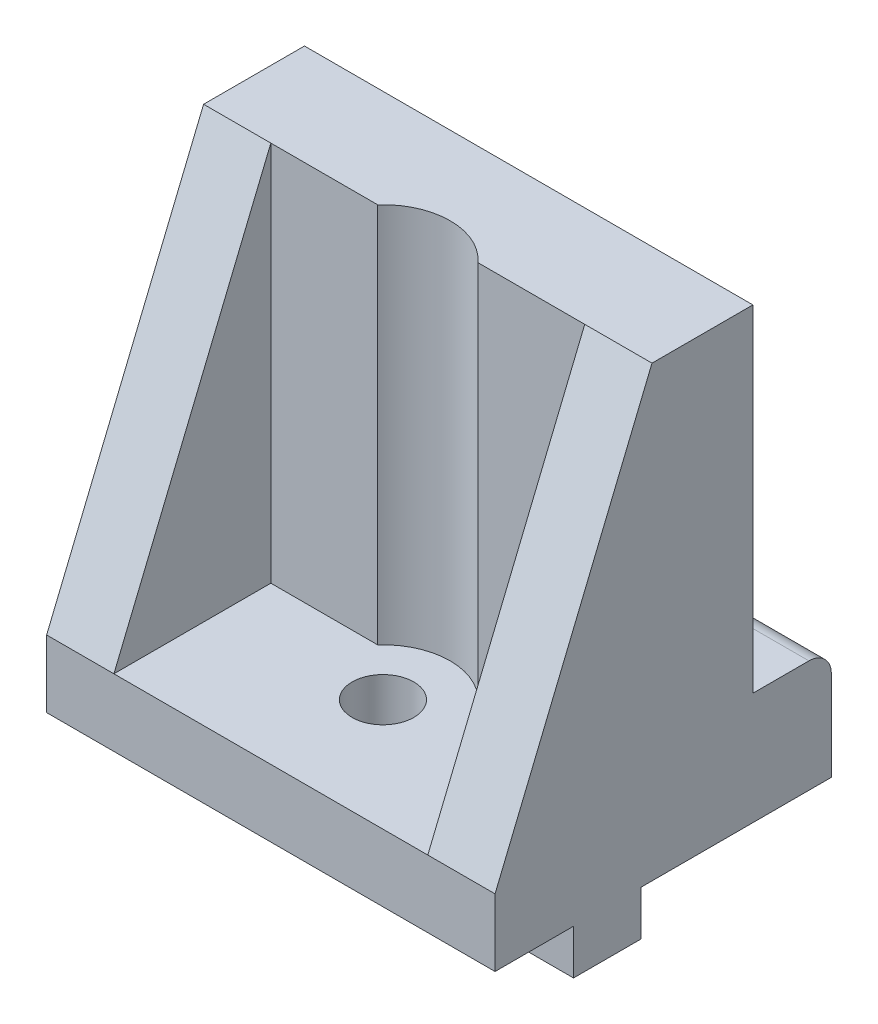
SolidWorks part; units mm, degrees
ref_plane "Alzado" through (0, 0, 0) normal (0, 0, 1) x (1, 0, 0)
ref_plane "Planta" through (0, 0, 0) normal (0, 1, 0) x (1, 0, 0)
ref_plane "Vista lateral" through (0, 0, 0) normal (1, 0, 0) x (0, 0, -1)
sketch "Croquis1" plane through (0, 0, 0) normal (0, 0, 1) x (1, 0, 0)
  line L1 (0, 0) -> (40, 0)
  line L2 (0, 0) -> (0, -40)
  line L3 (0, -40) -> (40, -40)
  line L4 (40, 0) -> (40, -40)
  dimension "D1" = 40
  dimension "D2" = 40
extrude "Saliente-Extruir1" add sketch "Croquis1" along normal blind 20
sketch "Croquis2" plane through (0, 0, 0) normal (0, 1, 0) x (1, 0, 0)
  line L0 (40, -20) -> (0, -20) construction
  line L1 (6, -20) -> (34, -20)
  line L2 (6, -20) -> (6, -6)
  line L3 (6, -6) -> (34, -6)
  line L4 (34, -20) -> (34, -6)
  line L5 (0, -20) -> (0, 0) construction
  line L6 (40, -20) -> (40, 0) construction
  line L7 (40, 0) -> (0, 0) construction
  dimension "D1" = 6
  dimension "D2" = 6
  dimension "D3" = 6
extrude "Cortar-Extruir1" cut sketch "Croquis2" against normal blind 34
sketch "Croquis3" plane through (0, 0, 0) normal (-1, 0, 0) x (0, 0, 1)
  line L0 (20, 0) -> (20, -34)
  line L1 (20, 0) -> (20, -40) construction
  line L2 (20, -34) -> (6, 0)
  line L3 (20, 0) -> (0, 0) construction
  line L4 (6, 0) -> (20, 0)
  dimension "D1" = 14
  dimension "D2" = 34
extrude "Cortar-Extruir2" cut sketch "Croquis3" against normal up to surface (40 mm away) up to face at (40, -20, 10)
sketch "Croquis7" plane through (0, -40, 0) normal (0, -1, 0) x (1, 0, 0)
  line L0 (0, 20) -> (0, 0) construction
  line L1 (0, 13) -> (40, 13)
  line L2 (0, 13) -> (0, 7)
  line L3 (0, 7) -> (40, 7)
  line L4 (40, 13) -> (40, 7)
  line L5 (40, 20) -> (40, 0) construction
  point P8 (0, 10)
  dimension "D1" = 6
  dimension "D2" = 10
extrude "Saliente-Extruir2" add sketch "Croquis7" along normal blind 1
sketch "Croquis8" plane through (0, -41, 0) normal (0, -1, 0) x (1, 0, 0)
  line L0 (0, 20) -> (40, 20) construction
  line L1 (0, 0) -> (40, 0) construction
  circle A0 centre (20, 10) radius 2.75
  point P4 (25.8595, 10)
  point P7 (20, 0)
  dimension "D2" = 5.5
  dimension "D1" = 10
  dimension "D3" = 0
extrude "Cortar-Extruir6" cut sketch "Croquis8" against normal up to surface (7 mm away) up to face at (20, -34, 13)
sketch "Croquis9" plane through (0, -34, 0) normal (0, 1, 0) x (1, 0, 0)
  circle A0 centre (20, -10) radius 6
  dimension "D1" = 12
extrude "Cortar-Extruir7" cut sketch "Croquis9" along normal up to surface (34 mm away) up to face at (20, 0, 4)
sketch "Croquis10" plane through (0, -41, 0) normal (0, -1, 0) x (1, 0, 0)
  line L0 (0, 7) -> (40, 7) construction
  line L1 (0, 13) -> (10, 13)
  line L2 (0, 13) -> (0, 7)
  line L3 (0, 7) -> (10, 7)
  line L4 (10, 13) -> (10, 7)
  line L6 (40, 13) -> (30, 13)
  line L7 (40, 13) -> (40, 7)
  line L8 (40, 7) -> (30, 7)
  line L9 (30, 13) -> (30, 7)
  dimension "D1" = 10
  dimension "D2" = 10
extrude "Saliente-Extruir3" add sketch "Croquis10" along normal blind 3
fillet "Redondeo1" radius 2 2 edges at (30, -41, 10) (10, -41, 10)
sketch "Croquis12" plane through (0, 0, 0) normal (-1, 0, 0) x (0, 0, 1)
  line L0 (0, -40) -> (-10, -40)
  line L1 (-10, -40) -> (-10, -30)
  line L2 (-10, -30) -> (-3, -30)
  line L3 (-3, -30) -> (-3, 0)
  line L4 (-3, 0) -> (0, 0)
  line L5 (0, 0) -> (0, -40)
  dimension "D1" = 3
  dimension "D2" = 10
  dimension "D3" = 10
extrude "Saliente-Extruir5" add sketch "Croquis12" against normal up to surface (40 mm away) up to face at (40, -31.3333, 9.5556)
fillet "Redondeo2" radius 2 1 edges at (20, -30, -10)
